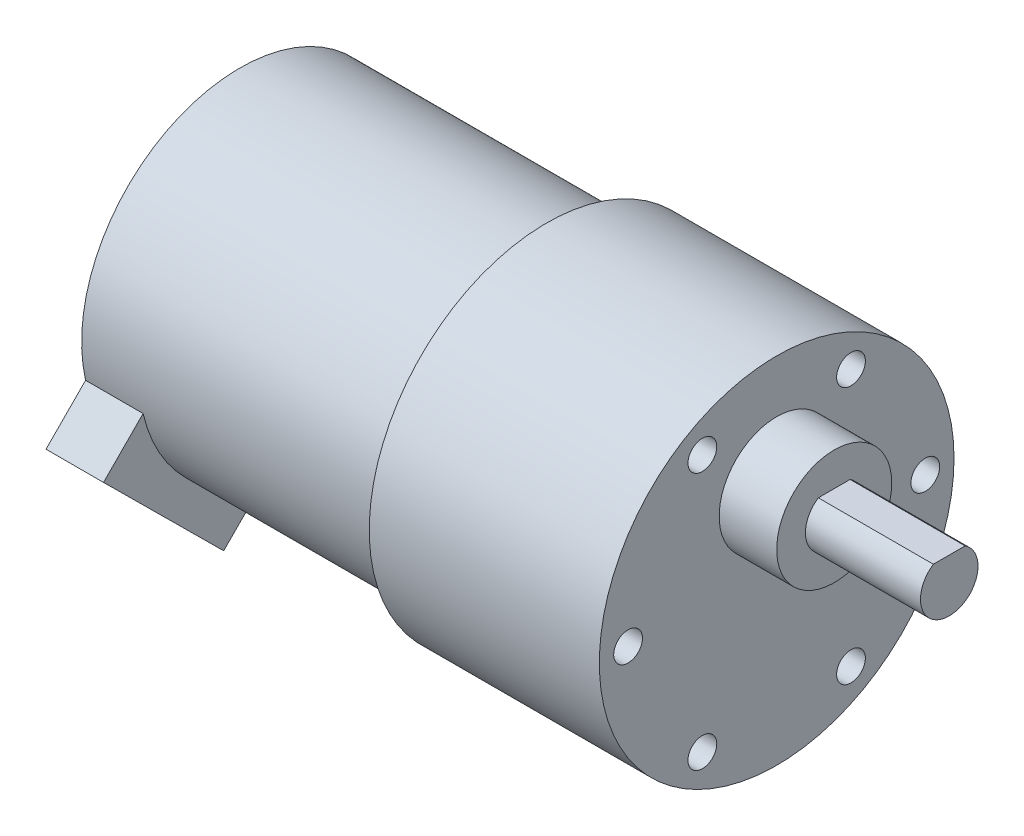
SolidWorks part; units mm, degrees
ref_plane "前视基准面" through (0, 0, 0) normal (0, 0, 1) x (1, 0, 0)
ref_plane "上视基准面" through (0, 0, 0) normal (0, 1, 0) x (1, 0, 0)
ref_plane "右视基准面" through (0, 0, 0) normal (1, 0, 0) x (0, 0, -1)
sketch "草图1" plane through (0, 0, 0) normal (1, 0, 0) x (0, 0, -1)
  circle A0 centre (0, 0) radius 18.5
  dimension "D1" = 37
extrude "凸台-拉伸1" add sketch "草图1" along normal blind 24
sketch "草图2" plane through (0, 0, 0) normal (-1, 0, 0) x (0, 0, 1)
  circle A0 centre (0, 0) radius 16.5
  dimension "D1" = 33
extrude "凸台-拉伸2" add sketch "草图2" along normal blind 32
sketch "草图4" plane through (24, 0, 0) normal (1, 0, 0) x (0, 0, -1)
  circle A0 centre (0, 0) radius 15.5 construction
  circle A1 centre (15.5, 0) radius 1.5
  circle A2 centre (7.75, -13.4234) radius 1.5
  circle A3 centre (-7.75, -13.4234) radius 1.5
  circle A4 centre (-15.5, 0) radius 1.5
  circle A5 centre (-7.75, 13.4234) radius 1.5
  circle A6 centre (7.75, 13.4234) radius 1.5
  point P18 (0, 0)
  dimension "D1" = 31
  dimension "D2" = 3
  dimension "D3" = 6
extrude "切除-拉伸1" cut sketch "草图4" against normal blind 6
sketch "草图5" plane through (24, 0, 0) normal (1, 0, 0) x (0, 0, -1)
  line L0 (0, 0) -> (0, 18.5) construction
  circle A0 centre (0, 0) radius 18.5 construction
  circle A1 centre (0, 7) radius 6
  dimension "D1" = 7
  dimension "D2" = 12
extrude "凸台-拉伸3" add sketch "草图5" along normal blind 6
sketch "草图6" plane through (30, 0, 0) normal (1, 0, 0) x (0, 0, -1)
  line L0 (-3, 7) -> (3, 7) construction
  line L1 (-1.6583, 9.5) -> (1.6583, 9.5)
  arc A0 (-1.6583, 9.5) -> (1.6583, 9.5) centre (0, 7) ccw
  dimension "D1" = 6
  dimension "D2" = 2.5
extrude "凸台-拉伸4" add sketch "草图6" along normal blind 12
sketch "草图7" plane through (-32, 0, 0) normal (-1, 0, 0) x (0, 0, 1)
  line L0 (0, 0) -> (13.9488, -14.0524) construction
  line L1 (7.6809, -20.2742) -> (20.2168, -7.8307)
  line L2 (20.2168, -7.8307) -> (16.0867, -3.6699)
  line L3 (16.0867, -3.6699) -> (3.5508, -16.1134)
  line L4 (3.5508, -16.1134) -> (7.6809, -20.2742)
  circle A1 centre (0, 0) radius 16.5 construction
  point P7 (13.9488, -14.0524)
  dimension "D1" = 36.3
extrude "凸台-拉伸5" add sketch "草图7" against normal blind 6
